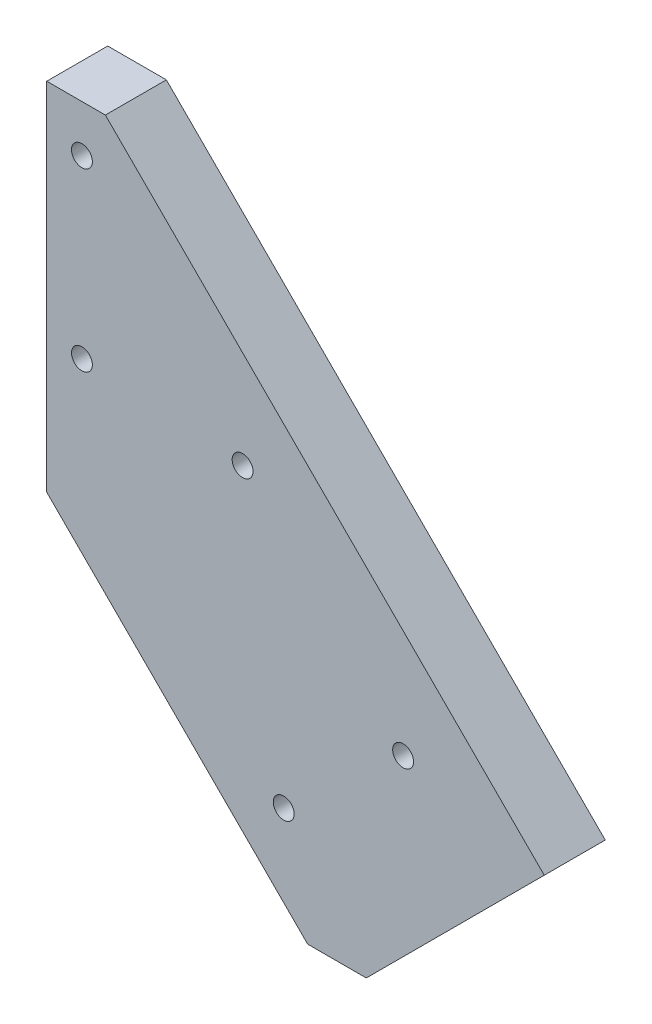
SolidWorks part; units mm, degrees
material "Acrylic (BLUE)"
ref_plane "Front Plane" through (0, 0, 0) normal (0, 0, 1) x (1, 0, 0)
ref_plane "Top Plane" through (0, 0, 0) normal (0, 1, 0) x (1, 0, 0)
ref_plane "Right Plane" through (0, 0, 0) normal (1, 0, 0) x (0, 0, -1)
sketch "Sketch1" plane through (0, 0, 0) normal (0, 0, 1) x (1, 0, 0)
  line L0 (6.35, -6.35) -> (53.8815, -53.8815)
  line L1 (53.8815, -53.8815) -> (31.4309, -76.3322)
  line L2 (31.4309, -76.3322) -> (0, -44.9013)
  line L3 (0, -44.9013) -> (0, -6.35)
  line L4 (0, 0) -> (95.1623, 0) construction
  line L5 (6.35, -6.35) -> (0, -6.35)
  dimension "D1" = 45
  dimension "D2" = 31.75
  dimension "D3" = 76.2
  dimension "D4" = 6.35
  dimension "D5" = 6.35
extrude "Boss-Extrude1" add sketch "Sketch1" along normal blind 6.604
hole_wizard "#4-40 Tapped Hole1" positions "Sketch3" profile "Sketch4" tap size "#4-40" standard "ANSI Inch"
sketch "Sketch3" plane through (0, 0, 6.604) normal (0, 0, 1) x (1, 0, 0)
  line L0 (21.2102, -31.7945) -> (38.593, -50.3147) construction
  line L2 (3.81, -30.48) -> (25.6633, -61.6897) construction
  line L5 (3.81, -11.43) -> (3.81, -30.48) construction
  line L7 (0, -6.35) -> (0, -44.9013) construction
  line L8 (6.35, -6.35) -> (0, -6.35) construction
  line L9 (38.593, -50.3147) -> (25.6633, -61.6897) construction
  line L10 (3.81, -30.48) -> (21.2102, -31.7945) construction
  point P0 (3.81, -11.43)
  point P2 (3.81, -30.48)
  point P4 (25.6633, -61.6897)
  point P6 (21.2102, -31.7945)
  point P8 (38.593, -50.3147)
  point P30 (3.175, -6.35)
  dimension "D1" = 25.4
  dimension "D2" = 3.81
  dimension "D3" = 38.1
  dimension "D4" = 19.05
  dimension "D5" = 17.4498
  dimension "D6" = 52.1716
  dimension "D7" = 5.08
  dimension "D8" = 17.2212
  dimension "D9" = 145
sketch "Sketch4" plane through (3.81, -11.43, 6.604) normal (1, 0, 0) x (0, -1, 0)
  line L0 (0, 0) -> (0, 8.2738)
  line L1 (0, 8.2738) -> (1.1303, 7.5946)
  line L2 (1.1303, 7.5946) -> (1.1303, 0)
  line L5 (1.1303, 0) -> (0, 0)
  line L10 (0, 8.2738) -> (-1.1303, 7.5946) construction
  line L11 (0, -6.35) -> (0, 107.95) construction
  dimension "Tap Drill Dia." = 2.2606
  dimension "Tap Drill Depth" = 7.5946
  dimension "Drill Angle" = 118
sketch "Sketch5" plane through (0, 0, 6.604) normal (0, 0, 1) x (1, 0, 0)
  line L0 (34.6059, -73.1572) -> (28.2559, -73.1572)
  line L1 (31.4309, -76.3322) -> (53.8815, -53.8815) construction
  line L2 (0, -44.9013) -> (31.4309, -76.3322) construction
  line L3 (28.2559, -73.1572) -> (31.4309, -76.3322)
  line L4 (31.4309, -76.3322) -> (34.6059, -73.1572)
  line L5 (6.35, -6.35) -> (0, -6.35) construction
extrude "Cut-Extrude1" cut sketch "Sketch5" against normal through all
other "Move Face1" [suppressed] parameters "D1"=0.127
